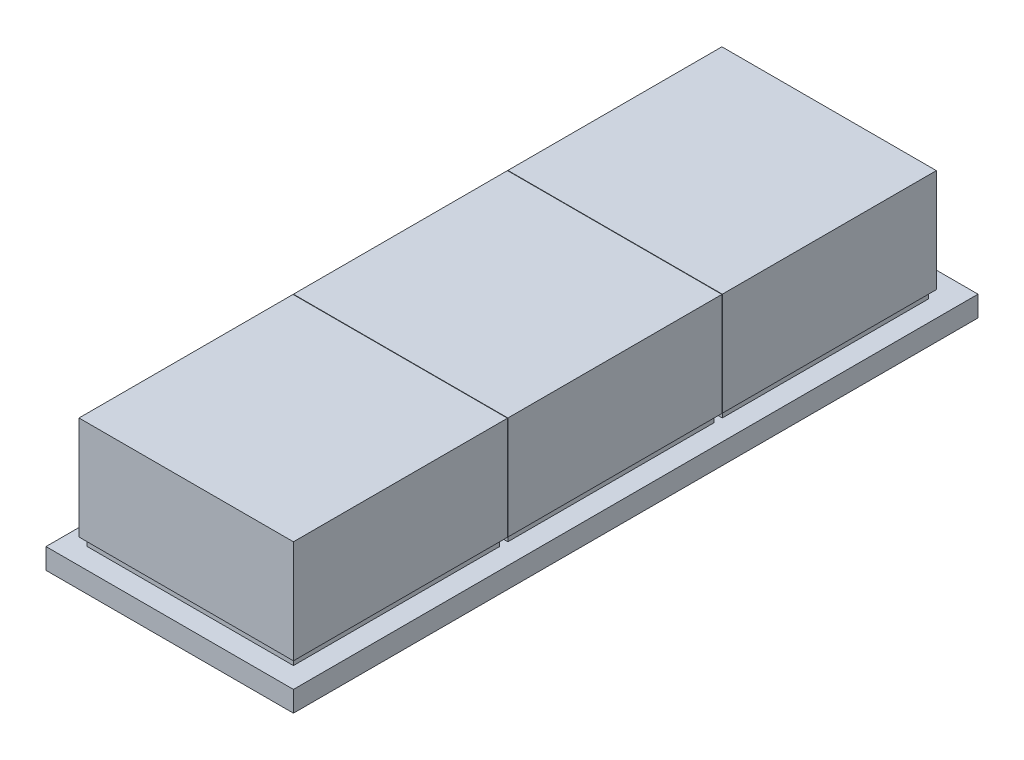
SolidWorks part; units mm, degrees
ref_plane "Front Plane" through (0, 0, 0) normal (0, 0, 1) x (1, 0, 0)
ref_plane "Top Plane" through (0, 0, 0) normal (0, 1, 0) x (1, 0, 0)
ref_plane "Right Plane" through (0, 0, 0) normal (1, 0, 0) x (0, 0, -1)
sketch "Sketch1" plane through (0, 0, 0) normal (0, 1, 0) x (1, 0, 0)
  line L1 (-30, -83) -> (30, -83)
  line L2 (-30, -83) -> (-30, 83)
  line L3 (-30, 83) -> (30, 83)
  line L4 (30, -83) -> (30, 83)
  line L5 (-30, -83) -> (30, 83) construction
  line L6 (-30, 83) -> (30, -83) construction
  point P0 (0, 0)
  dimension "D1" = 60
  dimension "D2" = 166
extrude "Boss-Extrude1" add sketch "Sketch1" along normal blind 5
sketch "Sketch2" plane through (0, 5, 0) normal (0, 1, 0) x (1, 0, 0)
  line L0 (0, 0) -> (0, -83) construction
  line L1 (-30, -83) -> (30, -83) construction
  line L3 (-25, -28) -> (25, -28)
  line L4 (-25, -28) -> (-25, -78)
  line L5 (-25, -78) -> (25, -78)
  line L6 (25, -28) -> (25, -78)
  line L7 (-25, -28) -> (25, -78) construction
  line L8 (-25, -78) -> (25, -28) construction
  point P5 (0, -53)
  dimension "D1" = 50
  dimension "D2" = 50
  dimension "D3" = 5
extrude "Boss-Extrude3" add sketch "Sketch2" along normal blind 2
pattern_linear "LPattern1" count 3 spacing 52 along (0, 0, -1) of "Boss-Extrude3"
sketch "Sketch3" plane through (0, 7, 0) normal (0, 1, 0) x (1, 0, 0)
  line L0 (0, 0) -> (0, -78) construction
  line L1 (-25, -78) -> (25, -78) construction
  line L3 (-26, -27.1) -> (26, -27.1)
  line L4 (-26, -27.1) -> (-26, -79)
  line L5 (-26, -79) -> (26, -79)
  line L6 (26, -27.1) -> (26, -79)
  line L7 (-26, -27.1) -> (26, -79) construction
  line L8 (-26, -79) -> (26, -27.1) construction
  line L9 (-30, -83) -> (30, -83) construction
  point P5 (0, -53.05)
  dimension "D1" = 52
  dimension "D2" = 51.9
  dimension "D3" = 4
extrude "Boss-Extrude8" add sketch "Sketch3" along normal blind 25
pattern_linear "LPattern5" count 3 spacing 52 along (0, 0, -1) of "Boss-Extrude8"
